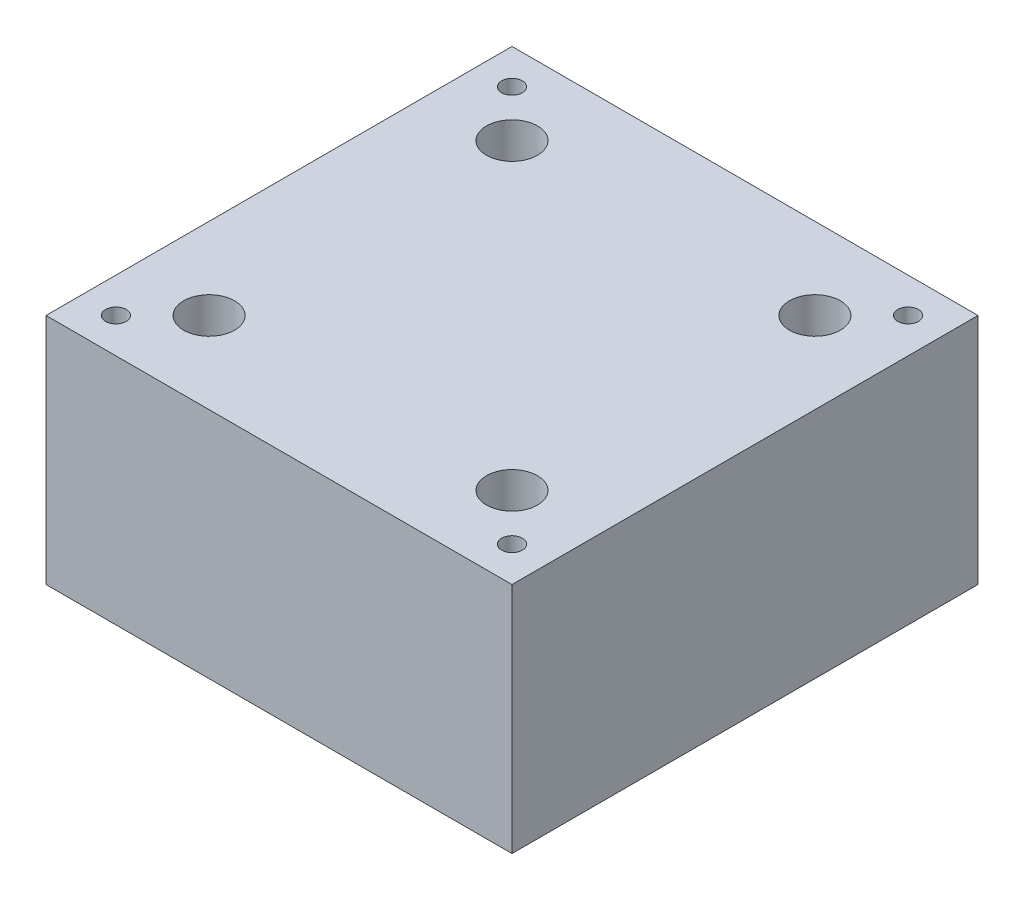
SolidWorks part; units mm, degrees
material "Delrin 2700 NC010, Low Viscosity Acetal Copolymer (SS)"
ref_plane "Front" through (0, 0, 0) normal (0, 0, 1) x (1, 0, 0)
ref_plane "Top" through (0, 0, 0) normal (0, 1, 0) x (1, 0, 0)
ref_plane "Right" through (0, 0, 0) normal (1, 0, 0) x (0, 0, -1)
sketch "Sketch1" plane through (0, 0, 0) normal (0, 1, 0) x (1, 0, 0)
  line L1 (-25.4, 25.4) -> (25.4, 25.4)
  line L2 (-25.4, 25.4) -> (-25.4, -25.4)
  line L3 (-25.4, -25.4) -> (25.4, -25.4)
  line L4 (25.4, 25.4) -> (25.4, -25.4)
  line L5 (-25.4, 25.4) -> (25.4, -25.4) construction
  line L6 (-25.4, -25.4) -> (25.4, 25.4) construction
  point P0 (0, 0)
  dimension "D1" = 50.8
  dimension "D2" = 50.8
extrude "Boss-Extrude1" add sketch "Sketch1" along normal blind 25.4
hole_wizard "#4-40 Tapped Hole1" positions "Sketch3" profile "Sketch2" tap size "#4-40" standard "ANSI Inch"
sketch "Sketch3" plane through (0, 25.4, 0) normal (0, 1, 0) x (1, 0, 0)
  point P0 (-21.59, 21.59)
  point P2 (21.59, 21.59)
  point P4 (21.59, -21.59)
  point P6 (-21.59, -21.59)
  dimension "D1" = 43.18
  dimension "D2" = 43.18
  dimension "D3" = 21.59
  dimension "D4" = 21.59
sketch "Sketch2" plane through (-21.59, 25.4, -21.59) normal (1, 0, 0) x (0, 0, 1)
  line L0 (0, 0) -> (0, 20.9738)
  line L1 (0, 20.9738) -> (1.1303, 20.2946)
  line L2 (1.1303, 20.2946) -> (1.1303, 0)
  line L5 (1.1303, 0) -> (0, 0)
  line L10 (0, 20.9738) -> (-1.1303, 20.2946) construction
  line L11 (0, -6.35) -> (0, 107.95) construction
  dimension "Tap Drill Dia." = 2.2606
  dimension "Tap Drill Depth" = 20.2946
  dimension "Drill Angle" = 118
hole_wizard "CBORE for #4 Socket Head Cap Screw1" positions "Sketch5" profile "Sketch4" counterbore size "#4" standard "ANSI Inch" end condition through all
sketch "Sketch5" plane through (0, 25.4, 0) normal (0, 1, 0) x (1, 0, 0)
  point P0 (-16.51, 16.51)
  point P2 (16.51, 16.51)
  point P4 (16.51, -16.51)
  point P6 (-16.51, -16.51)
  dimension "D1" = 33.02
  dimension "D2" = 33.02
  dimension "D3" = 16.51
  dimension "D4" = 16.51
sketch "Sketch4" plane through (-16.51, 25.4, -16.51) normal (1, 0, 0) x (0, 0, 1)
  line L0 (0, 0) -> (0, 25.4)
  line L1 (0, 25.4) -> (1.6319, 25.4)
  line L3 (1.6319, 25.4) -> (1.632, 7.9248)
  line L4 (1.632, 7.9248) -> (2.7788, 7.9248)
  line L5 (2.7788, 7.9248) -> (2.7788, 0)
  line L7 (2.7788, 0) -> (0, 0)
  line L11 (0, -6.35) -> (0, 107.95) construction
  dimension "Thru Hole Dia." = 3.2639
  dimension "Thru Hole Depth" = 25.4
  dimension "C'Bore Dia." = 5.5575
  dimension "C'Bore Depth" = 7.9248
